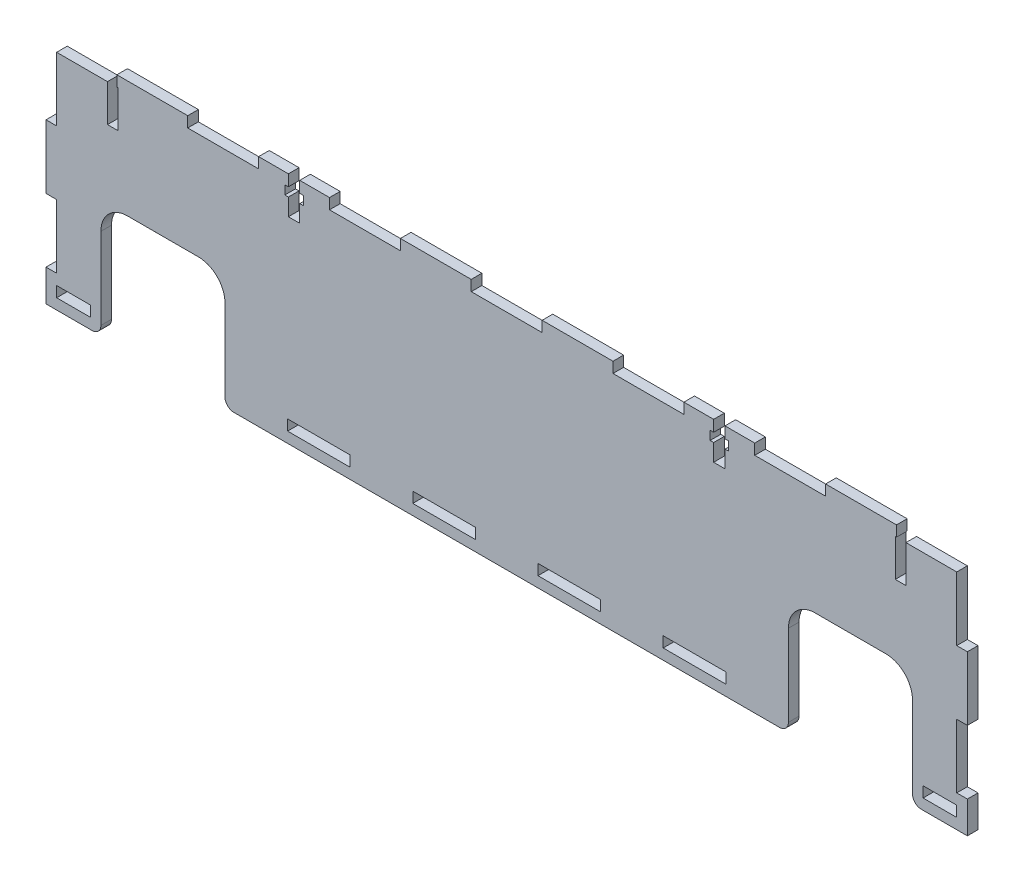
SolidWorks part; units mm, degrees
ref_plane "Front Plane" through (0, 0, 0) normal (0, 0, 1) x (1, 0, 0)
ref_plane "Top Plane" through (0, 0, 0) normal (0, 1, 0) x (1, 0, 0)
ref_plane "Right Plane" through (0, 0, 0) normal (1, 0, 0) x (0, 0, -1)
sketch "Sketch1" plane through (0, 0, 0) normal (0, 0, 1) x (1, 0, 0)
  line L0 (-130, 33) -> (130, 33)
  line L1 (130, 33) -> (130, -33)
  line L2 (130, -33) -> (114.5, -33)
  line L3 (114.5, -33) -> (114.5, 0)
  line L4 (114.5, 0) -> (79.5, 0)
  line L5 (79.5, 0) -> (79.5, -33)
  line L6 (79.5, -33) -> (-79.5, -33)
  line L7 (-79.5, -33) -> (-79.5, 0)
  line L8 (-79.5, 0) -> (-114.5, 0)
  line L9 (-114.5, 0) -> (-114.5, -33)
  line L10 (-114.5, -33) -> (-130, -33)
  line L11 (-130, -33) -> (-130, 33)
  point P14 (0, 33)
  point P15 (130, 0)
  dimension "D1" = 260
  dimension "D2" = 66
  dimension "D3" = 15.5
  dimension "D4" = 35
  dimension "D5" = 33
extrude "Boss-Extrude1" add sketch "Sketch1" along normal blind 3
sketch "Sketch2" plane through (0, 0, 3) normal (0, 0, 1) x (1, 0, 0)
  line L0 (-79.5, -30) -> (-61.8333, -30) construction
  line L1 (-61.8333, -30) -> (-44.1667, -30)
  line L2 (-61.8333, -30) -> (-61.8333, -27)
  line L3 (-61.8333, -27) -> (-44.1667, -27)
  line L4 (-44.1667, -30) -> (-44.1667, -27)
  line L5 (-61.8333, -30) -> (-44.1667, -27) construction
  line L6 (-61.8333, -27) -> (-44.1667, -30) construction
  line L7 (-26.5, -30) -> (-8.8333, -30)
  line L8 (-26.5, -30) -> (-26.5, -27)
  line L9 (-26.5, -27) -> (-8.8333, -27)
  line L10 (-8.8333, -30) -> (-8.8333, -27)
  line L11 (-26.5, -30) -> (-8.8333, -27) construction
  line L12 (-26.5, -27) -> (-8.8333, -30) construction
  line L13 (8.8333, -30) -> (26.5, -30)
  line L14 (8.8333, -30) -> (8.8333, -27)
  line L15 (8.8333, -27) -> (26.5, -27)
  line L16 (26.5, -30) -> (26.5, -27)
  line L17 (8.8333, -30) -> (26.5, -27) construction
  line L18 (8.8333, -27) -> (26.5, -30) construction
  line L19 (44.1667, -30) -> (61.8333, -30)
  line L20 (44.1667, -30) -> (44.1667, -27)
  line L21 (44.1667, -27) -> (61.8333, -27)
  line L22 (61.8333, -30) -> (61.8333, -27)
  line L23 (44.1667, -30) -> (61.8333, -27) construction
  line L24 (44.1667, -27) -> (61.8333, -30) construction
  line L25 (-79.5, 0) -> (-79.5, -33) construction
  line L26 (-44.1667, -30) -> (-26.5, -30) construction
  line L27 (-8.8333, -30) -> (8.8333, -30) construction
  line L28 (26.5, -30) -> (44.1667, -30) construction
  line L29 (61.8333, -30) -> (79.5, -30) construction
  line L30 (79.5, -33) -> (79.5, 0) construction
  line L31 (-79.5, -33) -> (79.5, -33) construction
  line L32 (114.5, -33) -> (130, -33) construction
  line L33 (-127, -30) -> (-117.5, -30)
  line L34 (-127, -30) -> (-127, -27)
  line L35 (-127, -27) -> (-117.5, -27)
  line L36 (-117.5, -30) -> (-117.5, -27)
  line L37 (-127, -30) -> (-117.5, -27) construction
  line L38 (-127, -27) -> (-117.5, -30) construction
  line L39 (117.5, -30) -> (127, -30)
  line L40 (117.5, -30) -> (117.5, -27)
  line L41 (117.5, -27) -> (127, -27)
  line L42 (127, -30) -> (127, -27)
  line L43 (117.5, -30) -> (127, -27) construction
  line L44 (117.5, -27) -> (127, -30) construction
  line L45 (-130, -33) -> (-114.5, -33) construction
  line L46 (-130, 33) -> (-130, -33) construction
  line L47 (-127, -24) -> (-130, -24)
  line L48 (-127, -24) -> (-127, -6)
  line L49 (-127, -6) -> (-130, -6)
  line L50 (-130, -24) -> (-130, -6)
  line L51 (-127, -24) -> (-130, -6) construction
  line L52 (-127, -6) -> (-130, -24) construction
  line L53 (-127, -6) -> (-127, 12) construction
  line L54 (-127, 12) -> (-130, 12)
  line L55 (-127, 12) -> (-127, 30)
  line L56 (-127, 30) -> (-130, 30)
  line L57 (-130, 12) -> (-130, 30)
  line L58 (-127, 12) -> (-130, 30) construction
  line L59 (-127, 30) -> (-130, 12) construction
  line L60 (-127, 30) -> (-127, 33) construction
  line L61 (130, 33) -> (-130, 33) construction
  line L62 (-127, -24) -> (-127, -27) construction
  line L63 (130, -33) -> (130, 33) construction
  line L64 (127, 12) -> (130, 12)
  line L65 (127, 12) -> (127, 30)
  line L66 (127, 30) -> (130, 30)
  line L67 (130, 12) -> (130, 30)
  line L68 (127, 12) -> (130, 30) construction
  line L69 (127, 30) -> (130, 12) construction
  line L70 (-110, 30) -> (-90, 30) construction
  line L71 (127, -24) -> (130, -24)
  line L72 (127, -24) -> (127, -6)
  line L73 (127, -6) -> (130, -6)
  line L74 (130, -24) -> (130, -6)
  line L75 (127, -24) -> (130, -6) construction
  line L76 (127, -6) -> (130, -24) construction
  line L77 (-110, 30) -> (-130, 30)
  line L78 (-110, 30) -> (-110, 33)
  line L79 (-110, 33) -> (-130, 33)
  line L80 (-130, 30) -> (-130, 33)
  line L81 (-110, 30) -> (-130, 33) construction
  line L82 (-110, 33) -> (-130, 30) construction
  line L83 (-90, 30) -> (-70, 30)
  line L84 (-90, 30) -> (-90, 33)
  line L85 (-90, 33) -> (-70, 33)
  line L86 (-70, 30) -> (-70, 33)
  line L87 (-90, 30) -> (-70, 33) construction
  line L88 (-90, 33) -> (-70, 30) construction
  line L89 (-50, 30) -> (-30, 30)
  line L90 (-50, 30) -> (-50, 33)
  line L91 (-50, 33) -> (-30, 33)
  line L92 (-30, 30) -> (-30, 33)
  line L93 (-50, 30) -> (-30, 33) construction
  line L94 (-50, 33) -> (-30, 30) construction
  line L95 (-10, 30) -> (10, 30)
  line L96 (-10, 30) -> (-10, 33)
  line L97 (-10, 33) -> (10, 33)
  line L98 (10, 30) -> (10, 33)
  line L99 (-10, 30) -> (10, 33) construction
  line L100 (-10, 33) -> (10, 30) construction
  line L101 (30, 30) -> (50, 30)
  line L102 (30, 30) -> (30, 33)
  line L103 (30, 33) -> (50, 33)
  line L104 (50, 30) -> (50, 33)
  line L105 (30, 30) -> (50, 33) construction
  line L106 (30, 33) -> (50, 30) construction
  line L107 (70, 30) -> (90, 30)
  line L108 (70, 30) -> (70, 33)
  line L109 (70, 33) -> (90, 33)
  line L110 (90, 30) -> (90, 33)
  line L111 (70, 30) -> (90, 33) construction
  line L112 (70, 33) -> (90, 30) construction
  line L113 (110, 30) -> (130, 30)
  line L114 (110, 30) -> (110, 33)
  line L115 (110, 33) -> (130, 33)
  line L116 (130, 30) -> (130, 33)
  line L117 (110, 30) -> (130, 33) construction
  line L118 (110, 33) -> (130, 30) construction
  line L119 (-70, 30) -> (-50, 30) construction
  line L120 (-30, 30) -> (-10, 30) construction
  line L121 (10, 30) -> (30, 30) construction
  line L122 (50, 30) -> (70, 30) construction
  line L123 (90, 30) -> (110, 30) construction
  point P0 (-53, -28.5)
  point P5 (-17.6667, -28.5)
  point P10 (17.6667, -28.5)
  point P15 (53, -28.5)
  point P28 (-122.25, -28.5)
  point P33 (122.25, -28.5)
  point P38 (-128.5, -15)
  point P41 (122.25, -33)
  point P44 (-122.25, -33)
  point P51 (-128.5, 21)
  point P56 (128.5, 21)
  point P66 (128.5, -15)
  point P71 (-120, 31.5)
  point P77 (-80, 31.5)
  point P82 (-40, 31.5)
  point P87 (0, 31.5)
  point P92 (40, 31.5)
  point P97 (80, 31.5)
  point P102 (120, 31.5)
  line M15 (-130, 33) -> (-130, -33)
  line M25 (130, -33) -> (130, 33)
  line M26 (130, 33) -> (-130, 33)
  dimension "D1" = 3
  dimension "D2" = 3
  dimension "D3" = 9.5
  dimension "D4" = 3
extrude "Cut-Extrude1" cut sketch "Sketch2" against normal through all both and the other way through all contours L55 L56 L54 M15 | L48 L49 L47 M15 | L1 L4 L3 L2 | L7 L10 L9 L8 | L13 L16 L15 L14 | L19 L22 L21 L20 | L39 L42 L41 L40 | L73 L72 L71 M25 | L66 L65 L64 M25 | L114 L113 L66 M25 M26 | L107 L110 L108 M26 | L101 L104 L102 M26 | L89 L92 L90 M26 | L83 L86 L84 M26 | L95 L98 L96 M26 | L79 L80 L77 L78 | L36 L35 L34 L33
sketch "Sketch3" plane through (0, 0, 3) normal (0, 0, 1) x (1, 0, 0)
  line L0 (-50, 33) -> (-70, 33) construction
  line L1 (-61.6, 22.5) -> (-58.4, 22.5)
  line L2 (-61.6, 22.5) -> (-61.6, 33)
  line L3 (-61.6, 33) -> (-58.4, 33)
  line L4 (-58.4, 22.5) -> (-58.4, 33)
  line L5 (-61.6, 22.5) -> (-58.4, 33) construction
  line L6 (-61.6, 33) -> (-58.4, 22.5) construction
  line L7 (70, 33) -> (50, 33) construction
  line L8 (58.4, 22.5) -> (61.6, 22.5)
  line L9 (58.4, 22.5) -> (58.4, 33)
  line L10 (58.4, 33) -> (61.6, 33)
  line L11 (61.6, 22.5) -> (61.6, 33)
  line L12 (58.4, 22.5) -> (61.6, 33) construction
  line L13 (58.4, 33) -> (61.6, 22.5) construction
  line L14 (-60, 33) -> (-60, 29.825) construction
  line L15 (-62.6, 29.825) -> (-57.4, 29.825)
  line L16 (-62.6, 29.825) -> (-62.6, 27.325)
  line L17 (-62.6, 27.325) -> (-57.4, 27.325)
  line L18 (-57.4, 29.825) -> (-57.4, 27.325)
  line L19 (-62.6, 29.825) -> (-57.4, 27.325) construction
  line L20 (-62.6, 27.325) -> (-57.4, 29.825) construction
  line L21 (57.4, 29.825) -> (62.6, 29.825)
  line L22 (57.4, 29.825) -> (57.4, 27.325)
  line L23 (57.4, 27.325) -> (62.6, 27.325)
  line L24 (62.6, 29.825) -> (62.6, 27.325)
  line L25 (57.4, 29.825) -> (62.6, 27.325) construction
  line L26 (57.4, 27.325) -> (62.6, 29.825) construction
  line L27 (60, 33) -> (60, 29.825) construction
  point P0 (-60, 27.75)
  point P7 (60, 27.75)
  point P14 (60, 33)
  point P15 (-60, 33)
  point P16 (-60, 28.575)
  point P21 (60, 28.575)
  dimension "D1" = 3.2
  dimension "D2" = 10.5
  dimension "D3" = 2.5
  dimension "D4" = 5.2
  dimension "D5" = 3.175
extrude "Cut-Extrude2" cut sketch "Sketch3" against normal through all both and the other way through all contours L4 L3 L2 L1 | L18 L17 L16 L15 | L8 L11 L10 L9 | L22 L23 L24 L21
fillet "Fillet1" radius 7.5 4 edges at (114.5, 0, 1.5) (79.5, 0, 1.5) (-79.5, 0, 1.5) (-114.5, 0, 1.5)
fillet "Fillet2" radius 2.5 4 edges at (114.5, -33, 1.5) (79.5, -33, 1.5) (-79.5, -33, 1.5) (-114.5, -33, 1.5)
sketch "Sketch4" plane through (0, 0, 0) normal (0, 0, 1) x (1, 0, 0)
  line L0 (-127, 30) -> (-110, 30) construction
  line L1 (-109.65, 19.5) -> (-112.65, 19.5)
  line L2 (-109.65, 19.5) -> (-109.65, 30)
  line L3 (-109.65, 30) -> (-112.65, 30)
  line L4 (-112.65, 19.5) -> (-112.65, 30)
  line L5 (-109.65, 19.5) -> (-112.65, 30) construction
  line L6 (-109.65, 30) -> (-112.65, 19.5) construction
  line L7 (-111.15, 24.75) -> (-127, 24.75) construction
  line L8 (109.65, 19.5) -> (112.65, 19.5)
  line L9 (109.65, 19.5) -> (109.65, 30)
  line L10 (109.65, 30) -> (112.65, 30)
  line L11 (112.65, 19.5) -> (112.65, 30)
  line L12 (109.65, 19.5) -> (112.65, 30) construction
  line L13 (109.65, 30) -> (112.65, 19.5) construction
  line L14 (-127, 30) -> (-127, 12) construction
  line L15 (111.15, 24.75) -> (127, 24.75) construction
  line L16 (127, 30) -> (127, 12) construction
  point P0 (-111.15, 24.75)
  point P7 (111.15, 24.75)
  point P20 (117.15, 21.2379)
  dimension "D1" = 14.35
  dimension "D2" = 3
  dimension "D3" = 10.5
extrude "Cut-Extrude3" cut sketch "Sketch4" against normal through all both and the other way through all
